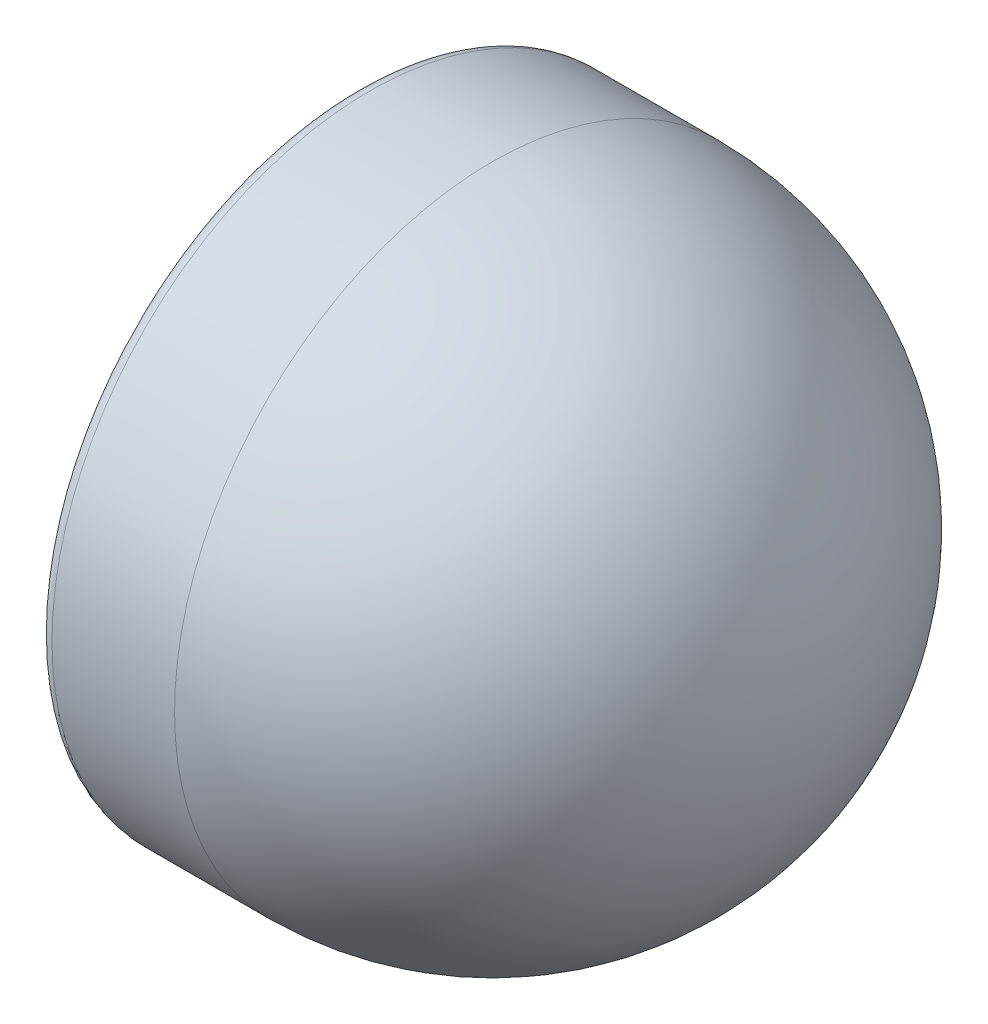
SolidWorks part; units mm, degrees
ref_plane "Front Plane" through (0, 0, 0) normal (0, 0, 1) x (1, 0, 0)
ref_plane "Top Plane" through (0, 0, 0) normal (0, 1, 0) x (1, 0, 0)
ref_plane "Right Plane" through (0, 0, 0) normal (1, 0, 0) x (0, 0, -1)
sketch "Sketch1" plane through (0, 0, 0) normal (0, 0, 1) x (1, 0, 0)
  line L0 (-70, 0) -> (75.1507, 0) construction
  line L1 (-70, 70) -> (-97, 70)
  line L2 (-100, 67) -> (-100, 61.5)
  line L3 (-98.5, 60) -> (-96.6213, 60)
  line L4 (-95.5607, 60.4393) -> (-92.0009, 63.9991)
  line L5 (-70, 69) -> (-97, 69)
  line L6 (-99, 67) -> (-99, 61.5)
  line L7 (-98.5, 61) -> (-96.6213, 61)
  line L8 (-96.2678, 61.1464) -> (-92.708, 64.7062)
  line L9 (-92.0009, 63.9991) -> (-92.0009, 64.7062)
  line L10 (-92.0009, 64.7062) -> (-92.708, 64.7062)
  line L11 (-1, 0) -> (0, 0)
  arc A0 (0, 0) -> (-70, 70) centre (-70, 0) ccw
  arc A1 (-97, 70) -> (-100, 67) centre (-97, 67) ccw
  arc A2 (-96.6213, 60) -> (-95.5607, 60.4393) centre (-96.6213, 61.5) ccw
  arc A3 (-100, 61.5) -> (-98.5, 60) centre (-98.5, 61.5) ccw
  arc A4 (-1, 0) -> (-70, 69) centre (-70, 0) ccw
  arc A5 (-97, 69) -> (-99, 67) centre (-97, 67) ccw
  arc A6 (-99, 61.5) -> (-98.5, 61) centre (-98.5, 61.5) ccw
  arc A7 (-96.6213, 61) -> (-96.2678, 61.1464) centre (-96.6213, 61.5) ccw
  point P11 (-100, 70)
  point P14 (-96, 60)
  point P17 (-100, 60)
  dimension "D1" = 70
  dimension "D6" = 3
  dimension "D7" = 1.5
  dimension "D2" = 30
  dimension "D3" = 10
  dimension "D4" = 4
  dimension "D5" = 135
  dimension "D9" = 6.9991
  dimension "D8" = 1
revolve "Revolve1" add sketch "Sketch1" angle 360 about L11
